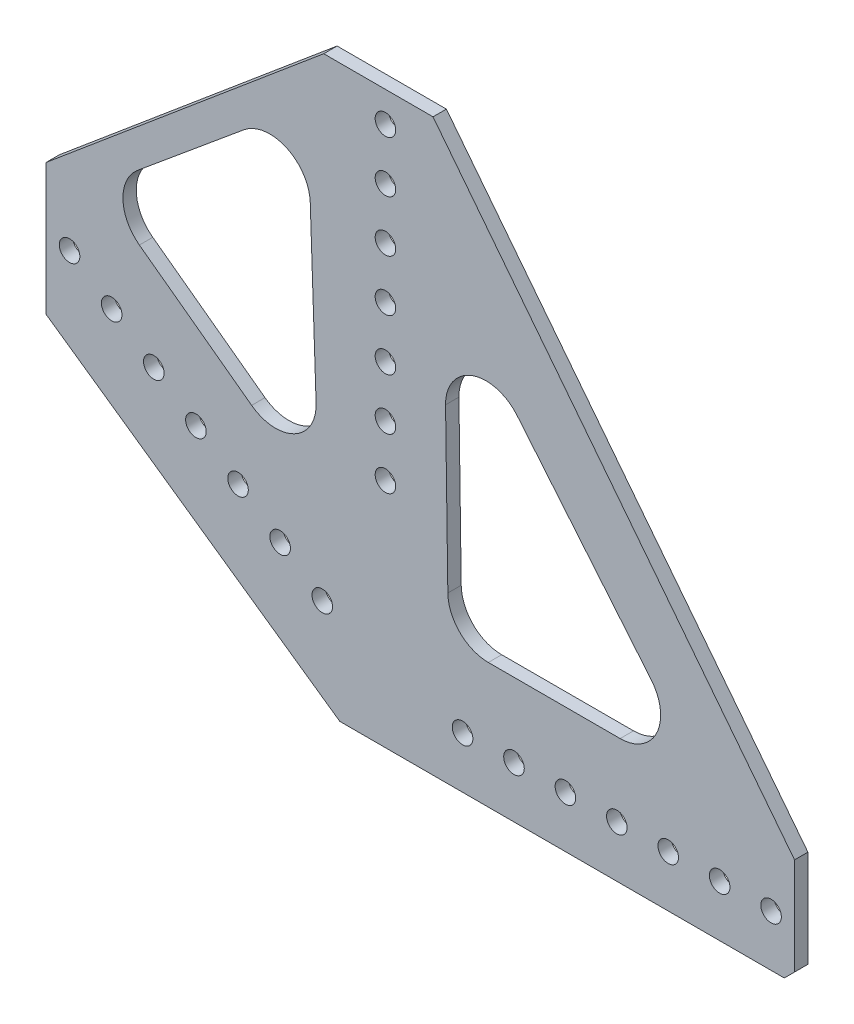
SolidWorks part; units mm, degrees
ref_plane "Front Plane" through (0, 0, 0) normal (0, 0, 1) x (1, 0, 0)
ref_plane "Top Plane" through (0, 0, 0) normal (0, 1, 0) x (1, 0, 0)
ref_plane "Right Plane" through (0, 0, 0) normal (1, 0, 0) x (0, 0, -1)
sketch "Sketch1" plane through (0, 0, 0) normal (0, 0, 1) x (1, 0, 0)
  line L0 (-280.0652, 184.4073) -> (-30.3877, 9.5812)
  line L1 (0, 0) -> (431.8, 0)
  line L2 (0, 0) -> (0, 25.4)
  line L3 (0, 25.4) -> (431.8, 25.4)
  line L4 (431.8, 0) -> (431.8, 25.4)
  line L5 (-280.0652, 184.4073) -> (-265.4964, 205.2137)
  line L6 (-30.3877, 9.5812) -> (-15.8188, 30.3877)
  line L7 (-265.4964, 205.2137) -> (-15.8188, 30.3877)
  line L8 (-25.4, 50.8) -> (0, 50.8)
  line L9 (-25.4, 50.8) -> (-25.4, 355.6)
  line L10 (0, 50.8) -> (0, 355.6)
  line L11 (-25.4, 355.6) -> (0, 355.6)
  line L12 (-225.8432, 161.9445) -> (23.8343, -12.8816) construction
  line L13 (0, 12.7) -> (431.8, 12.7) construction
  line L14 (-12.7, 12.7) -> (-12.7, 105.3379) construction
  line L15 (-12.7, 57.15) -> (-12.7, 69.85) construction
  line L16 (6.35, 12.7) -> (19.05, 12.7) construction
  line L17 (-28.3048, 23.6266) -> (-38.7081, 30.9111) construction
  line L19 (-96.5213, 140.8392) -> (88.3494, 140.8392)
  line L20 (-96.5213, 140.8392) -> (-96.5213, 0)
  line L21 (-96.5213, 0) -> (88.3494, 0)
  line L22 (88.3494, 140.8392) -> (88.3494, 0)
  circle A0 centre (-12.7, 57.15) radius 2.54
  circle A1 centre (-12.7, 69.85) radius 2.54
  circle A2 centre (-12.7, 82.55) radius 2.54
  circle A3 centre (-12.7, 95.25) radius 2.54
  circle A4 centre (-12.7, 107.95) radius 2.54
  circle A5 centre (-12.7, 120.65) radius 2.54
  circle A6 centre (-12.7, 133.35) radius 2.54
  circle A7 centre (-12.7, 146.05) radius 2.54
  circle A8 centre (-12.7, 158.75) radius 2.54
  circle A9 centre (-12.7, 171.45) radius 2.54
  circle A10 centre (-12.7, 184.15) radius 2.54
  circle A11 centre (-12.7, 196.85) radius 2.54
  circle A12 centre (-12.7, 209.55) radius 2.54
  circle A13 centre (-12.7, 222.25) radius 2.54
  circle A14 centre (-12.7, 234.95) radius 2.54
  circle A15 centre (-12.7, 247.65) radius 2.54
  circle A16 centre (-12.7, 260.35) radius 2.54
  circle A17 centre (-12.7, 273.05) radius 2.54
  circle A18 centre (-12.7, 285.75) radius 2.54
  circle A19 centre (-12.7, 298.45) radius 2.54
  circle A20 centre (-12.7, 311.15) radius 2.54
  circle A21 centre (-12.7, 323.85) radius 2.54
  circle A22 centre (-12.7, 336.55) radius 2.54
  circle A23 centre (-12.7, 349.25) radius 2.54
  circle A24 centre (6.35, 12.7) radius 2.54
  circle A25 centre (19.05, 12.7) radius 2.54
  circle A26 centre (31.75, 12.7) radius 2.54
  circle A27 centre (44.45, 12.7) radius 2.54
  circle A28 centre (57.15, 12.7) radius 2.54
  circle A29 centre (69.85, 12.7) radius 2.54
  circle A30 centre (82.55, 12.7) radius 2.54
  circle A31 centre (95.25, 12.7) radius 2.54
  circle A32 centre (107.95, 12.7) radius 2.54
  circle A33 centre (120.65, 12.7) radius 2.54
  circle A34 centre (133.35, 12.7) radius 2.54
  circle A35 centre (146.05, 12.7) radius 2.54
  circle A36 centre (158.75, 12.7) radius 2.54
  circle A37 centre (171.45, 12.7) radius 2.54
  circle A38 centre (184.15, 12.7) radius 2.54
  circle A39 centre (196.85, 12.7) radius 2.54
  circle A40 centre (209.55, 12.7) radius 2.54
  circle A41 centre (222.25, 12.7) radius 2.54
  circle A42 centre (234.95, 12.7) radius 2.54
  circle A43 centre (247.65, 12.7) radius 2.54
  circle A44 centre (260.35, 12.7) radius 2.54
  circle A45 centre (273.05, 12.7) radius 2.54
  circle A46 centre (285.75, 12.7) radius 2.54
  circle A47 centre (298.45, 12.7) radius 2.54
  circle A48 centre (311.15, 12.7) radius 2.54
  circle A49 centre (323.85, 12.7) radius 2.54
  circle A50 centre (336.55, 12.7) radius 2.54
  circle A51 centre (349.25, 12.7) radius 2.54
  circle A52 centre (361.95, 12.7) radius 2.54
  circle A53 centre (374.65, 12.7) radius 2.54
  circle A54 centre (387.35, 12.7) radius 2.54
  circle A55 centre (400.05, 12.7) radius 2.54
  circle A56 centre (412.75, 12.7) radius 2.54
  circle A57 centre (425.45, 12.7) radius 2.54
  circle A58 centre (-28.3048, 23.6266) radius 2.54
  circle A59 centre (-38.7081, 30.9111) radius 2.54
  circle A60 centre (-49.1113, 38.1955) radius 2.54
  circle A61 centre (-59.5145, 45.4799) radius 2.54
  circle A62 centre (-69.9178, 52.7643) radius 2.54
  circle A63 centre (-80.321, 60.0487) radius 2.54
  circle A64 centre (-90.7242, 67.3332) radius 2.54
  circle A65 centre (-101.1275, 74.6176) radius 2.54
  circle A66 centre (-111.5307, 81.902) radius 2.54
  circle A67 centre (-121.9339, 89.1864) radius 2.54
  circle A68 centre (-132.3372, 96.4708) radius 2.54
  circle A69 centre (-142.7404, 103.7553) radius 2.54
  circle A70 centre (-153.1436, 111.0397) radius 2.54
  circle A71 centre (-163.5468, 118.3241) radius 2.54
  circle A72 centre (-173.9501, 125.6085) radius 2.54
  circle A73 centre (-184.3533, 132.8929) radius 2.54
  circle A74 centre (-194.7565, 140.1774) radius 2.54
  circle A75 centre (-205.1598, 147.4618) radius 2.54
  circle A76 centre (-215.563, 154.7462) radius 2.54
  circle A77 centre (-225.9662, 162.0306) radius 2.54
  circle A78 centre (-236.3695, 169.315) radius 2.54
  circle A79 centre (-246.7727, 176.5995) radius 2.54
  circle A80 centre (-257.1759, 183.8839) radius 2.54
  circle A81 centre (-267.5792, 191.1683) radius 2.54
  point P12 (-23.1032, 19.9844)
  point P17 (0, 12.7)
  point P19 (-12.7, 12.7)
  point P22 (-12.7, 50.8)
  point P197 (49.2548, 50.8)
  point P198 (55.7772, 0)
  point P199 (-74.0338, 74.6176)
  point P200 (-93.0513, 141.9628)
  point P201 (88.3494, 140.8392)
  point P202 (0, 0)
  point P203 (-96.5213, 0)
  dimension "D12" = 5.08
  dimension "D15" = 5.08
  dimension "D19" = 5.08
  dimension "D20" = 6.35
  dimension "D1" = 25.4
  dimension "D2" = 431.8
  dimension "D3" = 25.4
  dimension "D4" = 25.4
  dimension "D5" = 304.8
  dimension "D6" = 304.8
  dimension "D7" = 145
  dimension "D8" = 12.7
  dimension "D9" = 12.7
  dimension "D10" = 38.1
  dimension "D11" = 6.35
  dimension "D14" = 12.7
  dimension "D16" = 6.35
  dimension "D18" = 12.7
  dimension "D21" = 12.7
  dimension "D13" = 24
  dimension "D17" = 34
extrude "Boss-Extrude3" add sketch "Sketch1" along normal blind 3.302 contours L22 L19 L10 L8 L9 L20 L7 L6 L0 L21 L2 L3 | L19 L9 L8 L10 A6 A5 A4 A3 A2 A1 A0 | L7 L20 L0 L6 A64 A63 A62 A61 A60 A59 A58 | L22 L3 L2 L1 A30 A29 A28 A27 A26 A25 A24
chamfer "Chamfer5" distance 114.3 angle 38 1 edges at (88.3494, 140.8392, 1.651)
chamfer "Chamfer6" distance 50.8 angle 55 1 edges at (-96.5213, 0, 1.651)
chamfer "Chamfer7" distance 68.58 angle 40 1 edges at (-96.5213, 140.8392, 1.651)
chamfer "Chamfer10" distance 2.54 angle 45 1 edges at (88.3494, 0, 1.651)
sketch "Sketch2" plane through (0, 0, 3.302) normal (0, 0, 1) x (1, 0, 0)
  line L0 (-31.9677, 127.7321) -> (-83.7659, 84.7323)
  line L1 (-83.7659, 84.7323) -> (-29.1176, 44.4586)
  line L2 (-29.1176, 44.4586) -> (-31.9677, 127.7321)
  line L3 (1.7453, 109.1426) -> (2.8535, 30.9514)
  line L4 (2.8535, 30.9514) -> (66.5479, 30.9514)
  line L5 (66.5479, 30.9514) -> (1.7453, 109.1426)
  point P2 (1.383, 110.0117)
  point P7 (0, 0)
  point P9 (0, 0)
  point P10 (-31.9677, 128.5996)
extrude "Cut-Extrude1" cut sketch "Sketch2" against normal blind 3.302
fillet "Fillet1" radius 10 1 edges at (2.8535, 30.9514, 1.651)
fillet "Fillet2" radius 10 1 edges at (-29.1176, 44.4586, 1.651)
fillet "Fillet3" radius 10 1 edges at (66.5479, 30.9514, 1.651)
fillet "Fillet4" radius 10 1 edges at (1.7453, 109.1426, 1.651)
fillet "Fillet5" radius 10 1 edges at (-31.9677, 127.7321, 1.651)
fillet "Fillet6" radius 10 1 edges at (-83.7659, 84.7323, 1.651)
